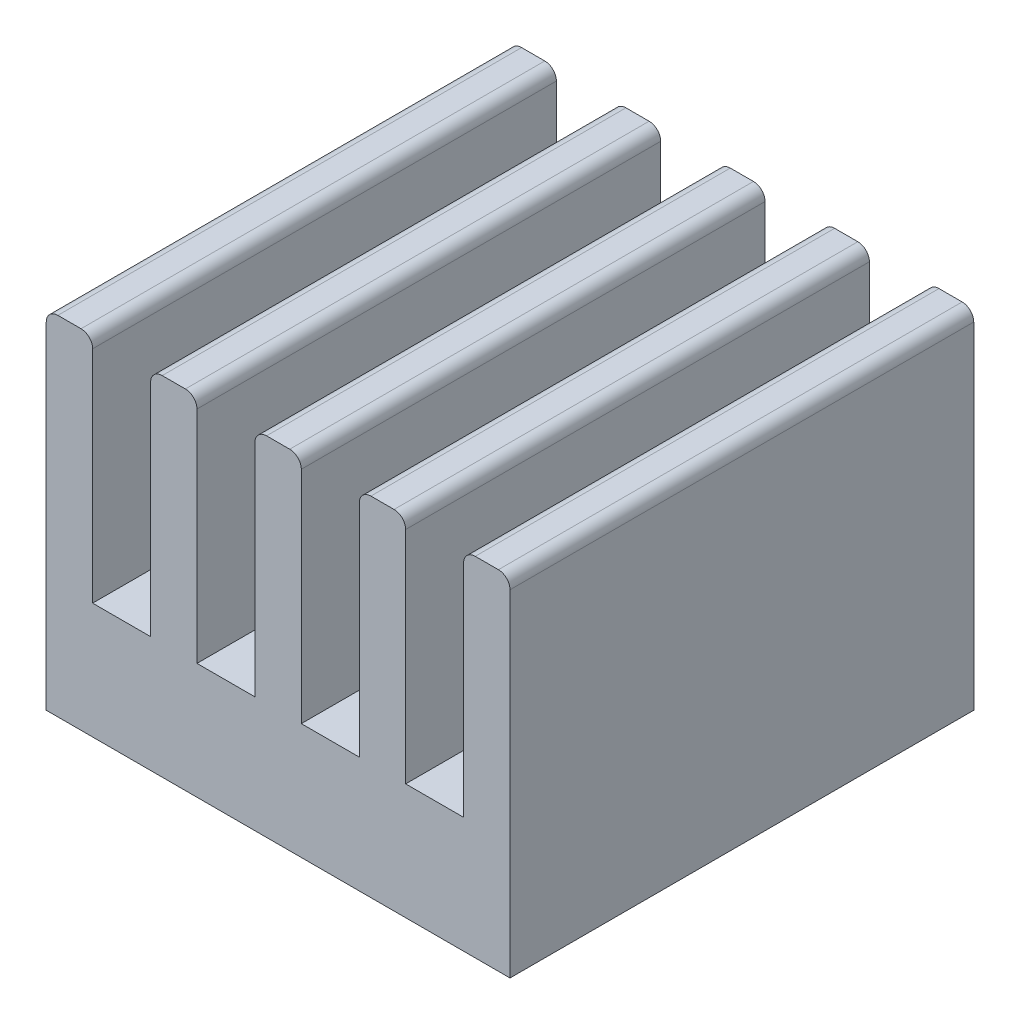
SolidWorks part; units mm, degrees
ref_plane "Front Plane" through (0, 0, 0) normal (0, 0, 1) x (1, 0, 0)
ref_plane "Top Plane" through (0, 0, 0) normal (0, 1, 0) x (1, 0, 0)
ref_plane "Right Plane" through (0, 0, 0) normal (1, 0, 0) x (0, 0, -1)
sketch "Sketch1" plane through (0, 0, 0) normal (0, 0, 1) x (1, 0, 0)
  line L0 (-4, 0) -> (4, 0)
  line L1 (-4, 0) -> (-4, 2) construction
  line L2 (-4, 2) -> (4, 2) construction
  line L3 (4, 2) -> (4, 0) construction
  line L4 (-4, 0) -> (-4, 6)
  line L5 (-4, 6) -> (-3.2, 6)
  line L6 (-3.2, 6) -> (-3.2, 2)
  line L7 (-3.2, 2) -> (-2.2, 2)
  line L8 (-2.2, 2) -> (-2.2, 6)
  line L9 (-2.2, 6) -> (-1.4, 6)
  line L10 (-1.4, 6) -> (-1.4, 2)
  line L11 (-1.4, 2) -> (-0.4, 2)
  line L12 (-0.4, 2) -> (-0.4, 6)
  line L13 (-0.4, 6) -> (0.4, 6)
  line L14 (0, 6) -> (0, 0) construction
  line L15 (0.4, 2) -> (0.4, 6)
  line L16 (1.4, 2) -> (0.4, 2)
  line L17 (1.4, 6) -> (1.4, 2)
  line L18 (2.2, 6) -> (1.4, 6)
  line L19 (2.2, 2) -> (2.2, 6)
  line L20 (3.2, 2) -> (2.2, 2)
  line L21 (3.2, 6) -> (3.2, 2)
  line L22 (4, 6) -> (3.2, 6)
  line L23 (4, 0) -> (4, 6)
  point P2 (0, 0)
  point P17 (0, 6)
  dimension "D1" = 8
  dimension "D2" = 2
  dimension "D3" = 1
  dimension "D4" = 6
extrude "Boss-Extrude1" add sketch "Sketch1" along normal blind 8
fillet "Fillet1" radius 0.2 10 edges at (-4, 6, 4) (-3.2, 6, 4) (-2.2, 6, 4) (-1.4, 6, 4) (-0.4, 6, 4) (0.4, 6, 4) (1.4, 6, 4) (2.2, 6, 4) (3.2, 6, 4) (4, 6, 4)
